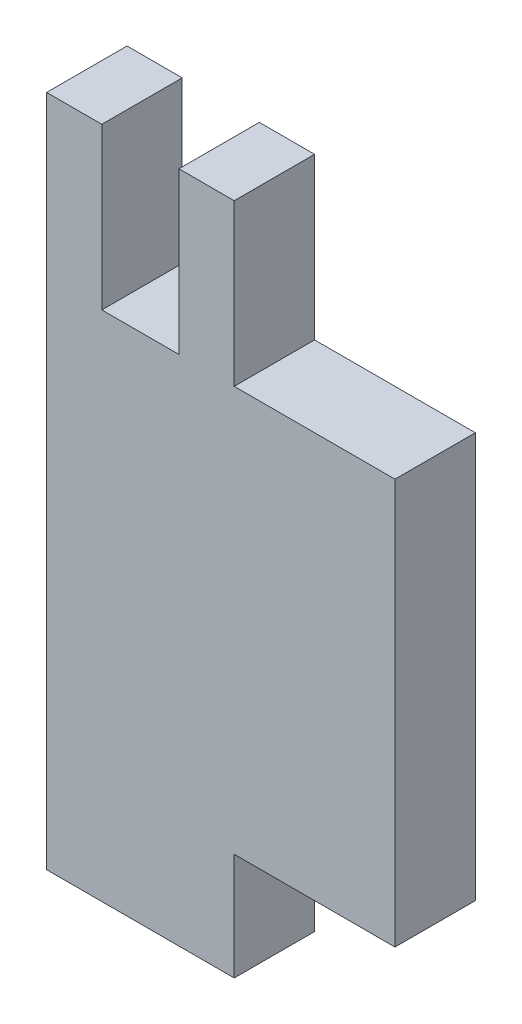
SolidWorks part; units mm, degrees
material "Arce"
ref_plane "Alzado" through (0, 0, 0) normal (0, 0, 1) x (1, 0, 0)
ref_plane "Planta" through (0, 0, 0) normal (0, 1, 0) x (1, 0, 0)
ref_plane "Vista lateral" through (0, 0, 0) normal (1, 0, 0) x (0, 0, -1)
sketch "Croquis1" plane through (0, 0, 0) normal (0, 0, 1) x (1, 0, 0)
  line L11 (7, 25.123) -> (7, 19.123)
  line L12 (7, 19.123) -> (13, 19.123)
  line L13 (13, 19.123) -> (13, 4)
  line L14 (13, 4) -> (7, 4)
  line L15 (7, 4) -> (7, 0)
  line L16 (7, 0) -> (0, 0)
  line L17 (0, 0) -> (0, 25.123)
  line L18 (2.06, 25.123) -> (0, 25.123)
  line L19 (2.06, 25.123) -> (4.937, 25.123)
  line L20 (2.06, 25.123) -> (2.06, 19.123)
  line L21 (2.06, 19.123) -> (4.937, 19.123)
  line L22 (4.937, 25.123) -> (4.937, 19.123)
  line L23 (0, 25.123) -> (4.937, 25.123)
  line L24 (4.937, 25.123) -> (7, 25.123)
  dimension "D1" = 15.123
  dimension "D2" = 4
  dimension "D3" = 6
  dimension "D4" = 7
  dimension "D6" = 2.877
  dimension "D7" = 6
  dimension "D9" = 2.06
extrude "Saliente-Extruir2" add sketch "Croquis1" along normal blind 3 contours L24 L22 L21 L20 L18 L17 L16 L15 L14 L13 L12 L11
